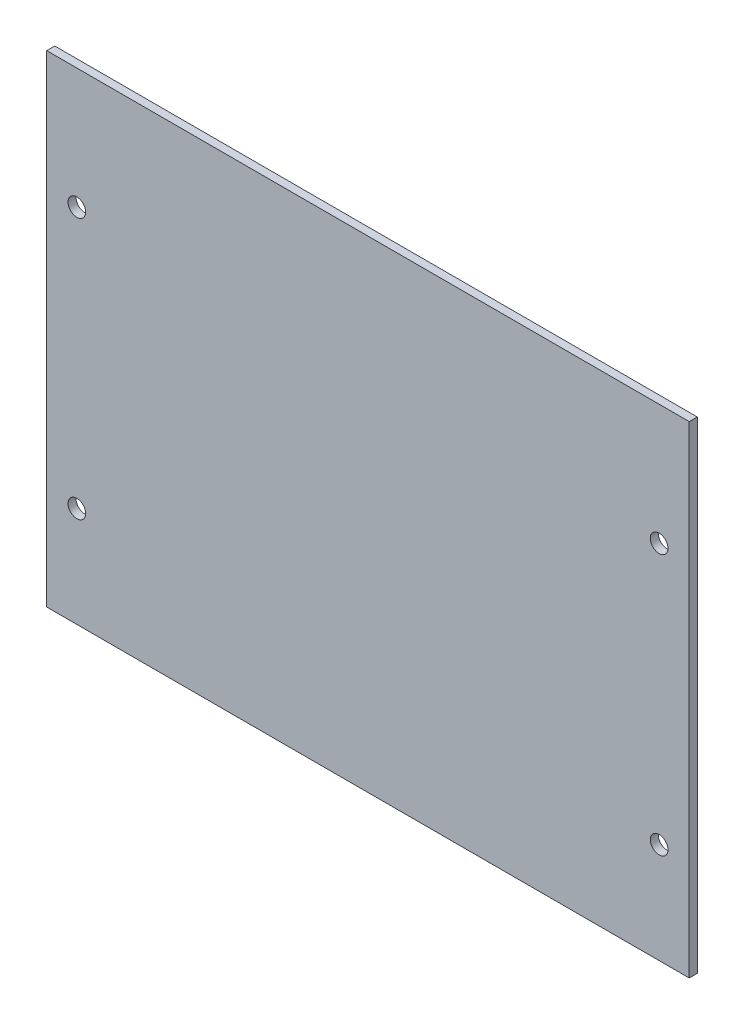
SolidWorks part; units mm, degrees
ref_plane "正面" through (0, 0, 0) normal (0, 0, 1) x (1, 0, 0)
ref_plane "平面" through (0, 0, 0) normal (0, 1, 0) x (1, 0, 0)
ref_plane "右側面" through (0, 0, 0) normal (1, 0, 0) x (0, 0, -1)
sketch "ｽｹｯﾁ1" plane through (0, 0, 0) normal (0, 0, 1) x (1, 0, 0)
  line L1 (-80, 60) -> (80, 60)
  line L2 (-80, 60) -> (-80, -60)
  line L3 (-80, -60) -> (80, -60)
  line L4 (80, 60) -> (80, -60)
  line L5 (-80, 60) -> (80, -60) construction
  line L6 (-80, -60) -> (80, 60) construction
  point P0 (0, 0)
  dimension "D1" = 160
  dimension "D2" = 120
extrude "ﾎﾞｽ - 押し出し1" add sketch "ｽｹｯﾁ1" along normal blind 2
sketch "ｽｹｯﾁ2" plane through (0, 0, 2) normal (0, 0, 1) x (1, 0, 0)
  line L0 (-80, -60) -> (-72.5, -60)
  line L1 (-80, -60) -> (80, -60) construction
  line L2 (-72.5, -60) -> (-72.5, -35)
  line L3 (-72.5, -35) -> (-72.5, 30)
  line L4 (80, -60) -> (72.5, -60)
  line L5 (72.5, -60) -> (72.5, -35)
  line L6 (72.5, -35) -> (72.5, 30)
  circle A0 centre (-72.5, -35) radius 2.2
  circle A1 centre (-72.5, 30) radius 2.2
  circle A2 centre (72.5, -35) radius 2.2
  circle A3 centre (72.5, 30) radius 2.2
  dimension "D5" = 4.4
  dimension "D6" = 4.4
  dimension "D7" = 4.4
  dimension "D8" = 4.4
  dimension "D1" = 7.5
  dimension "D2" = 7.5
  dimension "D3" = 25
  dimension "D4" = 25
  dimension "D9" = 65
  dimension "D10" = 65
extrude "ｶｯﾄ - 押し出し1" cut sketch "ｽｹｯﾁ2" against normal blind 2
